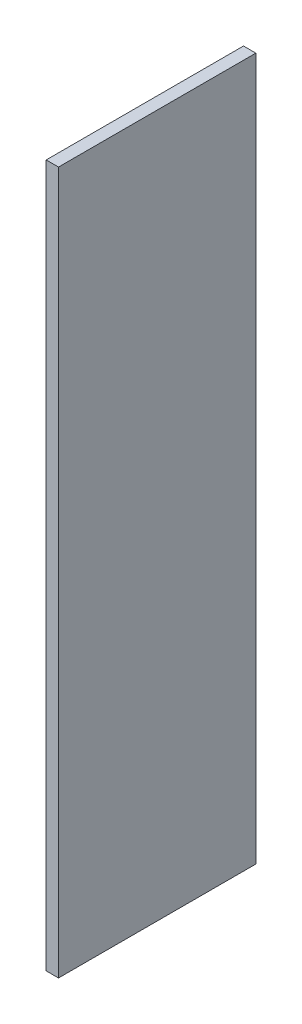
SolidWorks part; units mm, degrees
ref_plane "Front Plane" through (0, 0, 0) normal (0, 0, 1) x (1, 0, 0)
ref_plane "Top Plane" through (0, 0, 0) normal (0, 1, 0) x (1, 0, 0)
ref_plane "Right Plane" through (0, 0, 0) normal (1, 0, 0) x (0, 0, -1)
sketch "Sketch1" plane through (0, 0, 0) normal (1, 0, 0) x (0, 0, -1)
  line L1 (20.3921, -967.2196) -> (-267.6079, -967.2196)
  line L2 (20.3921, -967.2196) -> (20.3921, 57.7804)
  line L3 (20.3921, 57.7804) -> (-267.6079, 57.7804)
  line L4 (-267.6079, -967.2196) -> (-267.6079, 57.7804)
  line L5 (20.3921, -967.2196) -> (-267.6079, 57.7804) construction
  line L6 (20.3921, 57.7804) -> (-267.6079, -967.2196) construction
  point P0 (-123.6079, -454.7196)
  dimension "D1" = 288
  dimension "D2" = 1025
extrude "Boss-Extrude1" add sketch "Sketch1" along normal blind 18
equation "\"H_POLKI\"=1025"
equation "\"D2@Sketch1\"=\"H_POLKI\""
equation "\"DSP_WIDTH\"=18"
equation "\"D1@Boss-Extrude1\"=\"DSP_WIDTH\""
